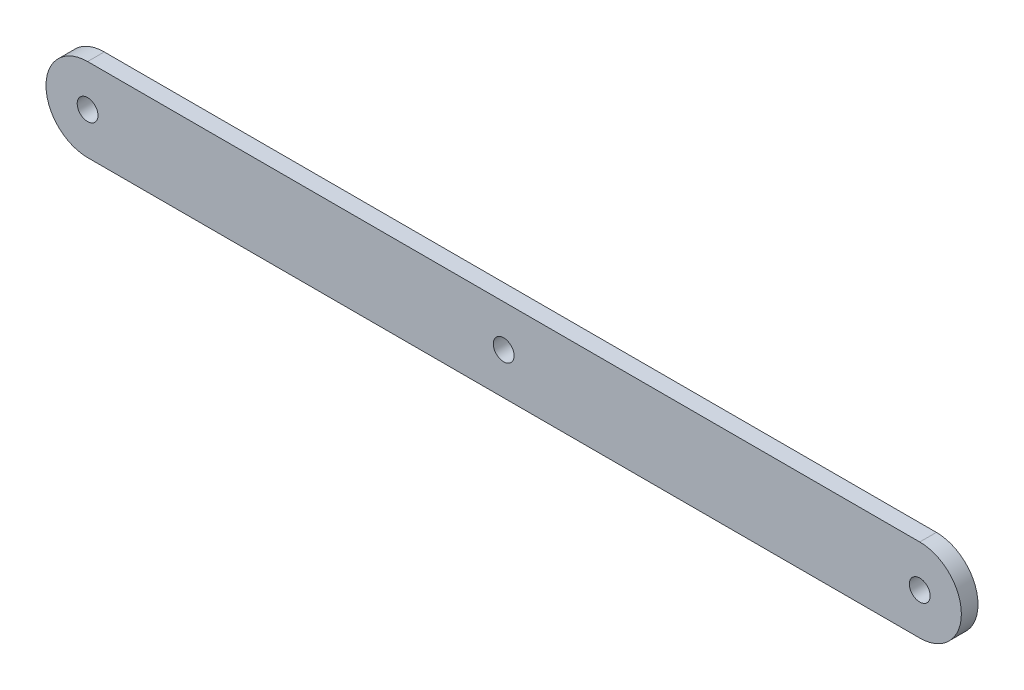
SolidWorks part; units mm, degrees
ref_plane "Front Plane" through (0, 0, 0) normal (0, 0, 1) x (1, 0, 0)
ref_plane "Top Plane" through (0, 0, 0) normal (0, 1, 0) x (1, 0, 0)
ref_plane "Right Plane" through (0, 0, 0) normal (1, 0, 0) x (0, 0, -1)
sketch "Sketch1" plane through (0, 0, 0) normal (0, 0, 1) x (1, 0, 0)
  line L0 (-12.4487, 1.1317) -> (12.4487, -1.1317) construction
  line L1 (-500, 50) -> (500, 50)
  line L3 (-500, -50) -> (500, -50)
  line L6 (-12.4487, -1.1317) -> (12.4487, 1.1317) construction
  circle A0 centre (-500, 0) radius 12.5
  circle A1 centre (500, 0) radius 12.5
  circle A2 centre (0, 0) radius 12.5
  arc A3 (-500, 50) -> (-500, -50) centre (-500, 0) ccw
  arc A4 (500, -50) -> (500, 50) centre (500, 0) ccw
  point P6 (0, 0)
  dimension "D3" = 25
  dimension "D1" = 1000
  dimension "D2" = 500
extrude "Boss-Extrude1" add sketch "Sketch1" along normal blind 20
